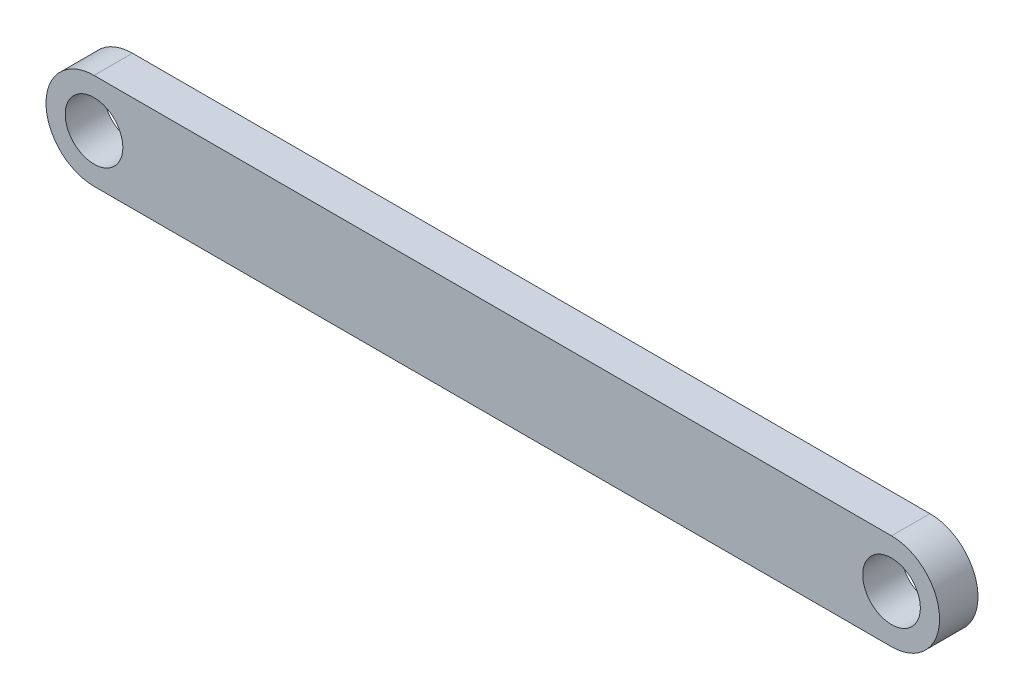
SolidWorks part; units mm, degrees
ref_plane "Front Plane" through (0, 0, 0) normal (0, 0, 1) x (1, 0, 0)
ref_plane "Top Plane" through (0, 0, 0) normal (0, 1, 0) x (1, 0, 0)
ref_plane "Right Plane" through (0, 0, 0) normal (1, 0, 0) x (0, 0, -1)
sketch "Sketch1" plane through (0, 0, 0) normal (0, 0, 1) x (1, 0, 0)
  line L0 (-0.0439, -0.016) -> (41.4561, -0.016) construction
  line L1 (-0.0439, 2.484) -> (41.4561, 2.484)
  line L2 (-0.0439, -2.516) -> (41.4561, -2.516)
  arc A0 (-0.0439, 2.484) -> (-0.0439, -2.516) centre (-0.0439, -0.016) ccw
  arc A1 (41.4561, -2.516) -> (41.4561, 2.484) centre (41.4561, -0.016) ccw
  circle A2 centre (-0.0439, -0.016) radius 1.5
  circle A3 centre (41.4561, -0.016) radius 1.5
  point P2 (20.7061, -0.016)
  dimension "D3" = 3
  dimension "D4" = 3
  dimension "D1" = 41.5
  dimension "D2" = 5
extrude "Boss-Extrude1" add sketch "Sketch1" along normal blind 2
